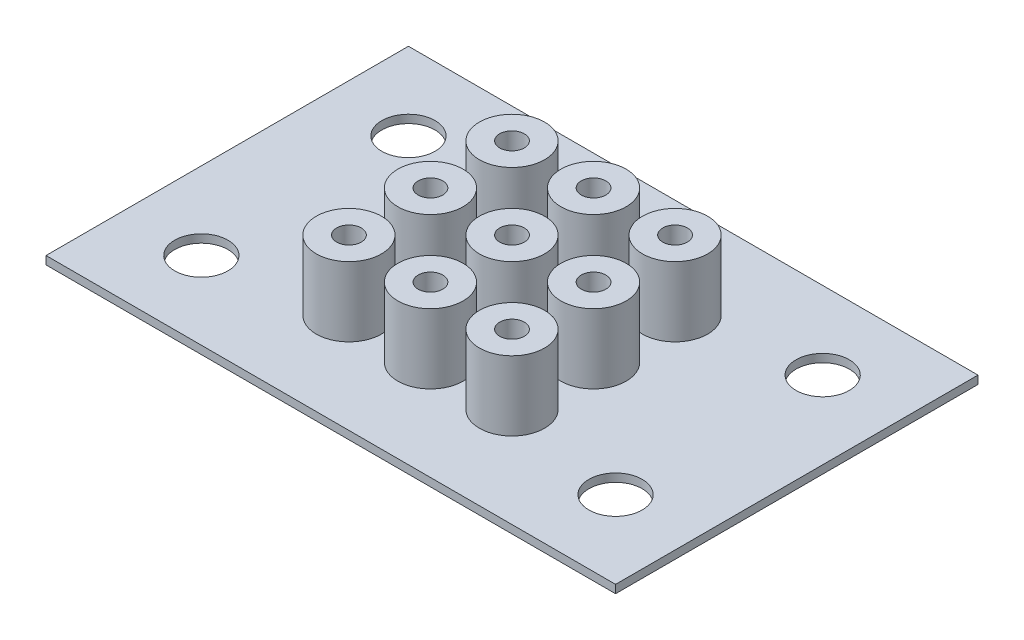
SolidWorks part; units mm, degrees
ref_plane "Front Plane" through (0, 0, 0) normal (0, 0, 1) x (1, 0, 0)
ref_plane "Top Plane" through (0, 0, 0) normal (0, 1, 0) x (1, 0, 0)
ref_plane "Right Plane" through (0, 0, 0) normal (1, 0, 0) x (0, 0, -1)
sketch "Sketch1" plane through (0, 0, 0) normal (0, 1, 0) x (1, 0, 0)
  line L0 (9.525, 34.925) -> (0, 34.925) construction
  line L1 (0, 0) -> (69.85, 0)
  line L2 (0, 0) -> (0, 44.45)
  line L3 (0, 44.45) -> (69.85, 44.45)
  line L4 (69.85, 0) -> (69.85, 44.45)
  line L5 (9.525, 34.925) -> (60.325, 34.925) construction
  line L6 (9.525, 34.925) -> (9.525, 9.525) construction
  line L7 (9.525, 9.525) -> (60.325, 9.525) construction
  line L8 (60.325, 34.925) -> (60.325, 9.525) construction
  line L9 (9.525, 34.925) -> (9.525, 44.45) construction
  line L10 (34.925, 22.225) -> (34.925, 32.225) construction
  circle A0 centre (9.525, 34.925) radius 3.2639
  circle A1 centre (60.325, 34.925) radius 3.2639
  circle A2 centre (9.525, 9.525) radius 3.2639
  circle A3 centre (60.325, 9.525) radius 3.2639
  circle A4 centre (34.925, 22.225) radius 1.25
  circle A5 centre (44.925, 22.225) radius 1.25
  circle A6 centre (44.925, 32.225) radius 1.25
  circle A7 centre (34.925, 32.225) radius 1.25
  circle A8 centre (24.925, 22.225) radius 1.25
  circle A9 centre (24.925, 32.225) radius 1.25
  circle A10 centre (34.925, 32.225) radius 1.25
  circle A11 centre (44.925, 22.225) radius 1.25
  circle A12 centre (44.925, 12.225) radius 1.25
  circle A13 centre (34.925, 12.225) radius 1.25
  circle A14 centre (24.925, 22.225) radius 1.25
  circle A15 centre (24.925, 12.225) radius 1.25
  circle A16 centre (34.925, 12.225) radius 1.25
  point P13 (34.925, 34.925)
  point P14 (34.925, 44.45)
  point P20 (69.85, 22.225)
  dimension "D5" = 6.5278
  dimension "D6" = 2.5
  dimension "D1" = 69.85
  dimension "D2" = 44.45
  dimension "D3" = 50.8
  dimension "D4" = 25.4
  dimension "D9" = 10
  dimension "D16" = 10
  dimension "D17" = 10
  dimension "D18" = 10
  dimension "D19" = 10
  dimension "D20" = 10
  dimension "D21" = 10
  dimension "D22" = 10
  dimension "D7" = 2
  dimension "D8" = 2
  dimension "D10" = 2
  dimension "D11" = 2
  dimension "D12" = 2
  dimension "D13" = 2
  dimension "D14" = 2
  dimension "D15" = 2
extrude "Boss-Extrude1" add sketch "Sketch1" along normal blind 1 contours L1 L4 L3 L2 A15 A13 A12 A9 A8 A7 A6 A5 A4 A3 A2 A1 A0
sketch "Sketch2" plane through (0, 1, 0) normal (0, 1, 0) x (1, 0, 0)
  line L0 (34.925, 22.225) -> (34.925, 32.225) construction
  circle A0 centre (34.925, 22.225) radius 4
  circle A1 centre (34.925, 22.225) radius 1.51
  circle A2 centre (44.925, 22.225) radius 4
  circle A3 centre (44.925, 22.225) radius 1.51
  circle A4 centre (44.925, 32.225) radius 4
  circle A5 centre (44.925, 32.225) radius 1.51
  circle A6 centre (34.925, 32.225) radius 4
  circle A7 centre (34.925, 32.225) radius 1.51
  circle A8 centre (44.925, 22.225) radius 1.51
  circle A9 centre (44.925, 22.225) radius 4
  circle A10 centre (44.925, 12.225) radius 1.51
  circle A11 centre (44.925, 12.225) radius 4
  circle A12 centre (34.925, 12.225) radius 1.51
  circle A13 centre (34.925, 12.225) radius 4
  circle A14 centre (24.925, 22.225) radius 4
  circle A15 centre (24.925, 22.225) radius 1.51
  circle A16 centre (24.925, 32.225) radius 4
  circle A17 centre (24.925, 32.225) radius 1.51
  circle A18 centre (34.925, 32.225) radius 4
  circle A19 centre (34.925, 32.225) radius 1.51
  circle A20 centre (24.925, 22.225) radius 1.51
  circle A21 centre (24.925, 22.225) radius 4
  circle A22 centre (24.925, 12.225) radius 1.51
  circle A23 centre (24.925, 12.225) radius 4
  circle A24 centre (34.925, 12.225) radius 1.51
  circle A25 centre (34.925, 12.225) radius 4
  dimension "D1" = 3.02
  dimension "D2" = 8
  dimension "D5" = 10
  dimension "D10" = 10
  dimension "D11" = 10
  dimension "D12" = 10
  dimension "D13" = 10
  dimension "D14" = 10
  dimension "D15" = 10
  dimension "D16" = 10
  dimension "D3" = 2
  dimension "D4" = 2
  dimension "D6" = 2
  dimension "D7" = 2
  dimension "D8" = 2
  dimension "D9" = 2
extrude "Boss-Extrude2" add sketch "Sketch2" along normal blind 8.525
